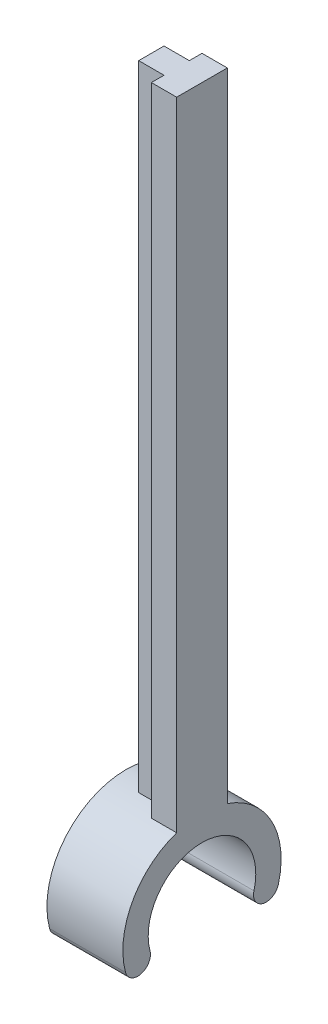
SolidWorks part; units mm, degrees
ref_plane "Front" through (0, 0, 0) normal (0, 0, 1) x (1, 0, 0)
ref_plane "Top" through (0, 0, 0) normal (0, 1, 0) x (1, 0, 0)
ref_plane "Right" through (0, 0, 0) normal (1, 0, 0) x (0, 0, -1)
sketch "Sketch1" plane through (0, 0, 0) normal (1, 0, 0) x (0, 0, -1)
  line L0 (0, 0) -> (-6.25, 0)
  line L1 (0, 0) -> (-6.037, -1.6176)
  line L2 (0, 50) -> (0, -50) construction
  line L3 (0, 0) -> (6.037, -1.6176)
  line L4 (-6.037, -1.6176) -> (-5.0711, -1.3588)
  circle A0 centre (0, 0) radius 4.25
  circle A1 centre (0, 0) radius 6.25
  arc A2 (-6.037, -1.6176) -> (-4.1052, -1.1) centre (-5.0711, -1.3588) ccw
  arc A3 (6.037, -1.6176) -> (4.1052, -1.1) centre (5.0711, -1.3588) cw
  dimension "D1" = 15
  dimension "D3" = 12.5
  dimension "D4" = 8.5
  dimension "D2" = 1
extrude "Boss-Extrude1" add sketch "Sketch1" against normal blind 4 and the other way blind 2 contours L3 A1 L0 A0 | A3 L3 | L0 A1 L1 A0 | L1 A2
sketch "Sketch2" plane through (0, 0, 0) normal (1, 0, 0) x (0, 0, -1)
  line L0 (0, 0) -> (0, 6.25)
  line L1 (0, 6.25) -> (0, 4.25)
  line L2 (0, 4.25) -> (-2, 4.25)
  line L4 (-2, 4.25) -> (2, 4.25)
  line L5 (-2, 4.25) -> (-2, 56.25)
  line L6 (-2, 56.25) -> (2, 56.25)
  line L7 (2, 4.25) -> (2, 56.25)
  arc A0 (6.037, -1.6176) -> (-6.037, -1.6176) centre (0, 0) ccw construction
  dimension "D1" = 2
  dimension "D2" = 2
  dimension "D3" = 4
  dimension "D4" = 52
extrude "Boss-Extrude2" add sketch "Sketch2" along normal blind 2
sketch "Sketch3" plane through (0, 0, 0) normal (1, 0, 0) x (0, 0, -1)
  line L0 (0, 56.25) -> (-1, 56.25)
  line L1 (-2, 56.25) -> (2, 56.25) construction
  line L3 (-1, 56.25) -> (1, 56.25)
  line L4 (-1, 56.25) -> (-1, 4.25)
  line L5 (-1, 4.25) -> (1, 4.25)
  line L6 (1, 56.25) -> (1, 4.25)
  dimension "D1" = 1
  dimension "D2" = 52
  dimension "D3" = 2
extrude "Boss-Extrude3" add sketch "Sketch3" against normal blind 2 contours L6 L3 L0 L4 L5
